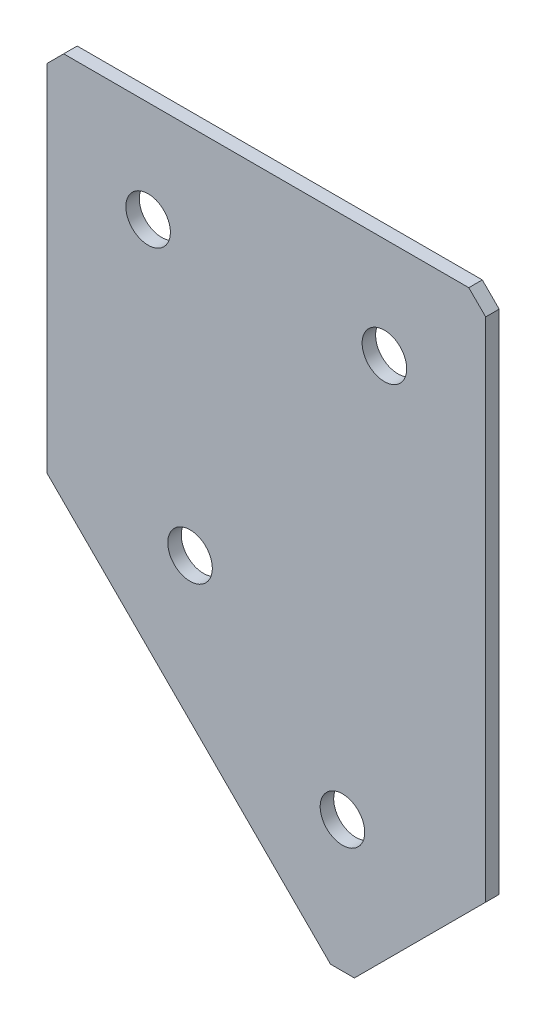
SolidWorks part; units mm, degrees
material "Простая углеродистая сталь"
ref_plane "Спереди" through (0, 0, 0) normal (0, 0, 1) x (1, 0, 0)
ref_plane "Сверху" through (0, 0, 0) normal (0, 1, 0) x (1, 0, 0)
ref_plane "Справа" through (0, 0, 0) normal (1, 0, 0) x (0, 0, -1)
sketch "Эскиз3" plane through (0, 0, 0) normal (0, 0, -1) x (1, 0, 0)
  line L0 (0, 0) -> (65, 0)
  line L1 (65, 0) -> (65, 77.5736)
  line L2 (0, 0) -> (0, 55)
  line L3 (0, 55) -> (43.7868, 98.7868)
  line L4 (43.7868, 98.7868) -> (65, 77.5736)
  dimension "D1" = 65
  dimension "D2" = 55
  dimension "D3" = 30
  dimension "D4" = 45
  dimension "D5" = 77.5736
extrude "Бобышка-Вытянуть1" add sketch "Эскиз3" along normal blind 2
hole_wizard "Отверстие с зазором M61" positions "Эскиз4" profile "Эскиз5" hole size "M6" standard "DIN" end condition through all
sketch "Эскиз4" plane through (0, 0, -2) normal (0, 0, -1) x (1, 0, 0)
  line L2 (43.7868, 98.7868) -> (0, 55) construction
  line L3 (15, 15) -> (50, 15) construction
  line L5 (0, 0) -> (65, 0) construction
  line L6 (0, 55) -> (0, 0) construction
  line L7 (65, 0) -> (65, 77.5736) construction
  line L8 (65, 77.5736) -> (43.7868, 98.7868) construction
  line L9 (21.2132, 55) -> (0, 33.7868) construction
  line L11 (54.3934, 88.1802) -> (-6.972, 26.8148) construction
  point P0 (15, 15)
  point P2 (50, 15)
  point P4 (21.2132, 55)
  point P6 (43.7868, 77.5736)
  dimension "D1" = 15
  dimension "D3" = 15
  dimension "D4" = 15
  dimension "D5" = 15
  dimension "D6" = 30
  dimension "D7" = 31.9239
  dimension "D8" = 35
  dimension "D9" = 15
sketch "Эскиз5" plane through (15, -15, -2) normal (1, 0, 0) x (0, 1, 0)
  line L0 (0, 0) -> (0, 2)
  line L1 (0, 2) -> (3.3, 2)
  line L2 (3.3, 2) -> (3.3, 0)
  line L5 (3.3, 0) -> (0, 0)
  line L11 (0, -6.35) -> (0, 107.95) construction
  dimension "Диаметр сквозного отверстия" = 6.6
  dimension "Глубина сквозного отверстия" = 2
chamfer "Фаска1" distance 2.5 distance2 2.5 3 edges at (43.7868, -98.7868, -1) (65, 0, -1) (0, 0, -1)
